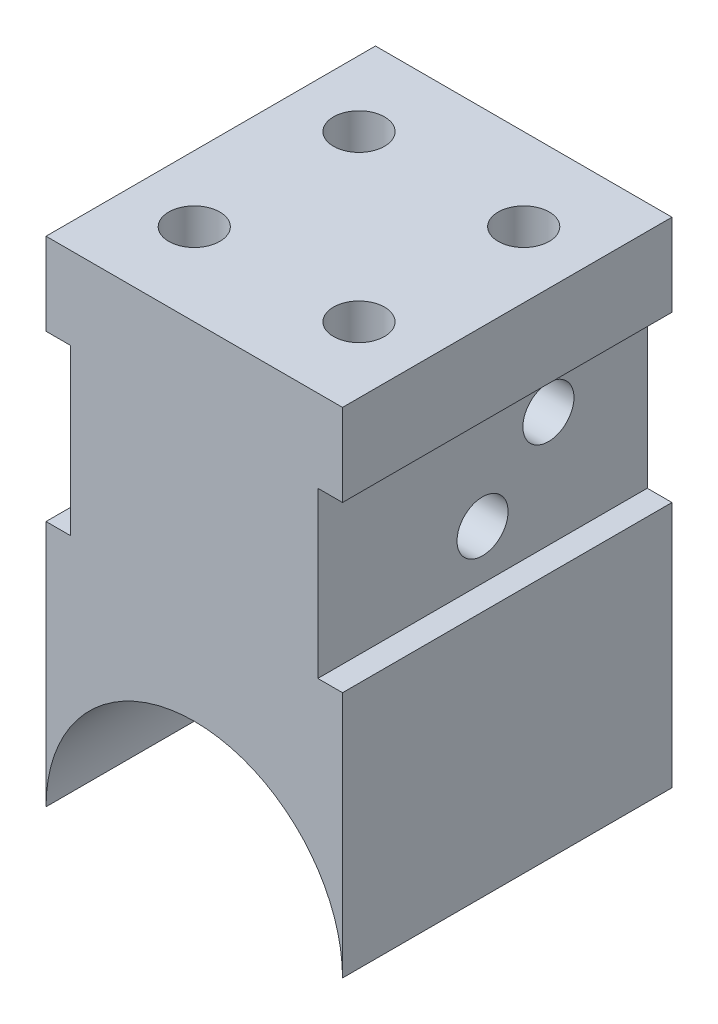
SolidWorks part; units mm, degrees
ref_plane "前视基准面" through (0, 0, 0) normal (0, 0, 1) x (1, 0, 0)
ref_plane "上视基准面" through (0, 0, 0) normal (0, 1, 0) x (1, 0, 0)
ref_plane "右视基准面" through (0, 0, 0) normal (1, 0, 0) x (0, 0, -1)
sketch "草图1" plane through (0, 0, 0) normal (0, 0, 1) x (1, 0, 0)
  line L0 (-9, 0) -> (-9, 30)
  line L1 (-9, 30) -> (9, 30)
  line L2 (9, 30) -> (9, 0)
  arc A0 (9, 0) -> (-9, 0) centre (0, 0) ccw
  dimension "D1" = 18
  dimension "D2" = 30
extrude "凸台-拉伸1" add sketch "草图1" along normal blind 20
sketch "草图2" plane through (-9, 0, 0) normal (-1, 0, 0) x (0, 0, 1)
  line L0 (0, 25) -> (20, 25)
  line L1 (0, 30) -> (0, 0) construction
  line L2 (20, 30) -> (20, 0) construction
  line L3 (20, 25) -> (20, 15)
  line L4 (20, 15) -> (0, 15)
  line L5 (0, 15) -> (0, 25)
  line L6 (20, 30) -> (0, 30) construction
  line L7 (20, 0) -> (0, 0) construction
  dimension "D1" = 5
  dimension "D2" = 15
extrude "切除-拉伸1" cut sketch "草图2" against normal blind 1.5
mirror "镜向1" about plane through (0, 0, 0) normal (1, 0, 0) of "切除-拉伸1"
sketch "草图3" plane through (7.5, 0, 0) normal (1, 0, 0) x (0, 0, -1)
  line L0 (0, 15) -> (-20, 15) construction
  line L1 (-20, 25) -> (0, 25) construction
  line L2 (-20, 15) -> (-20, 25) construction
  circle A0 centre (-6, 22) radius 1.55
  circle A1 centre (-10, 18) radius 1.55
  dimension "D1" = 3
  dimension "D5" = 3.1
  dimension "D6" = 3.1
  dimension "D2" = 3
  dimension "D3" = 10
  dimension "D4" = 14
extrude "切除-拉伸2" cut sketch "草图3" against normal up to surface (15 mm away) up to face at (-7.5, 20, 10)
sketch "草图4" plane through (0, 30, 0) normal (0, 1, 0) x (1, 0, 0)
  line L1 (9, -20) -> (9, 0) construction
  line L8 (9, 0) -> (-9, 0) construction
  circle A0 centre (-5, -5) radius 1.55
  circle A1 centre (5, -5) radius 1.55
  circle A2 centre (5, -15) radius 1.55
  circle A3 centre (-5, -15) radius 1.55
  point P2 (0, -10)
  point P19 (0, -10)
  dimension "D5" = 3.1
  dimension "D1" = 9
  dimension "D2" = 10
  dimension "D3" = 10
  dimension "D4" = 5
  dimension "D6" = 4
extrude "切除-拉伸5" cut sketch "草图4" against normal blind 5
sketch "草图6" plane through (0, 30, 0) normal (0, 1, 0) x (1, 0, 0)
  circle A2 centre (-5, -15) radius 1.55
  circle A3 centre (5, -15) radius 1.55
extrude "切除-拉伸6" cut sketch "草图6" against normal blind 10
